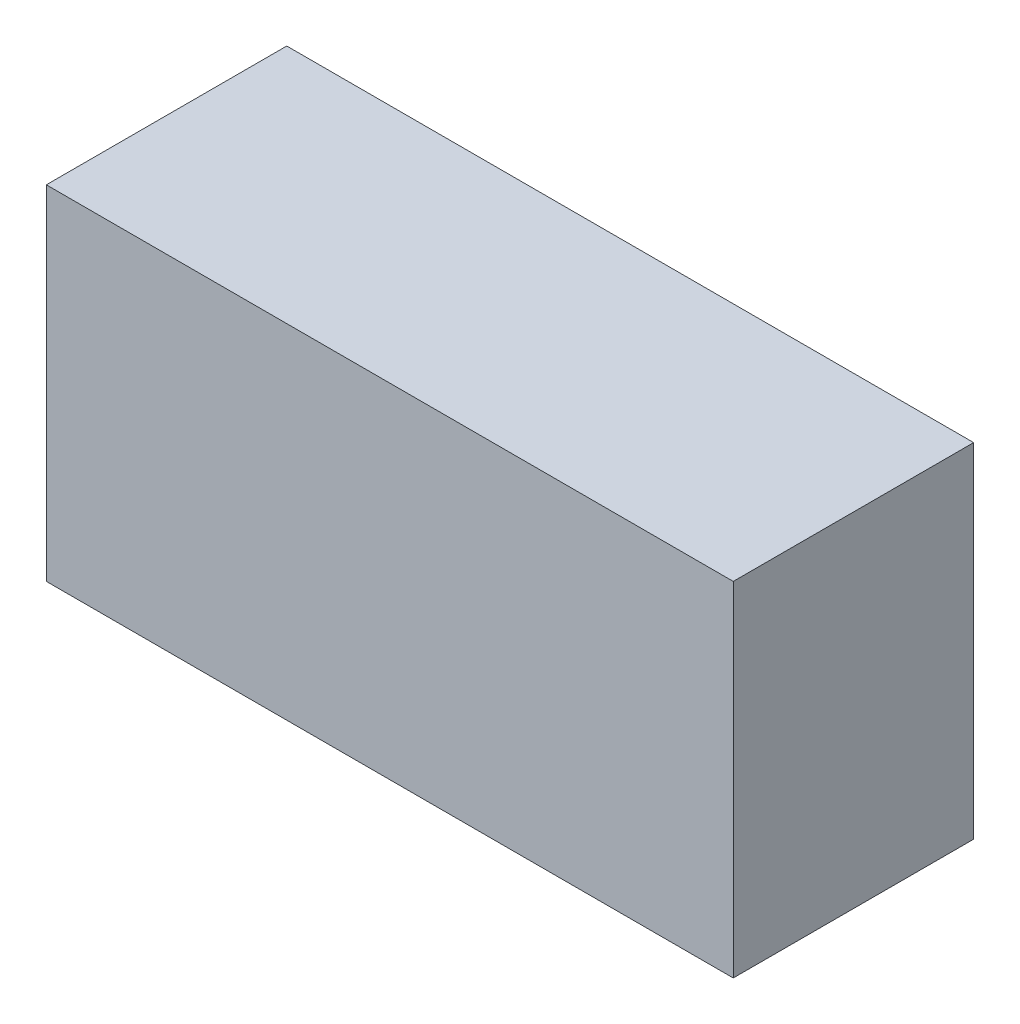
SolidWorks part; units mm, degrees
ref_plane "Front Plane" through (0, 0, 0) normal (0, 0, 1) x (1, 0, 0)
ref_plane "Top Plane" through (0, 0, 0) normal (0, 1, 0) x (1, 0, 0)
ref_plane "Right Plane" through (0, 0, 0) normal (1, 0, 0) x (0, 0, -1)
sketch "Sketch1" plane through (0, 0, 0) normal (0, 1, 0) x (1, 0, 0)
  line L1 (-500, 175) -> (500, 175)
  line L2 (-500, 175) -> (-500, -175)
  line L3 (-500, -175) -> (500, -175)
  line L4 (500, 175) -> (500, -175)
  line L5 (-500, 175) -> (500, -175) construction
  line L6 (-500, -175) -> (500, 175) construction
  point P0 (0, 0)
  dimension "D1" = 350
  dimension "D2" = 1000
extrude "Boss-Extrude1" add sketch "Sketch1" along normal blind 500 contours L2 L1 L4 L3
